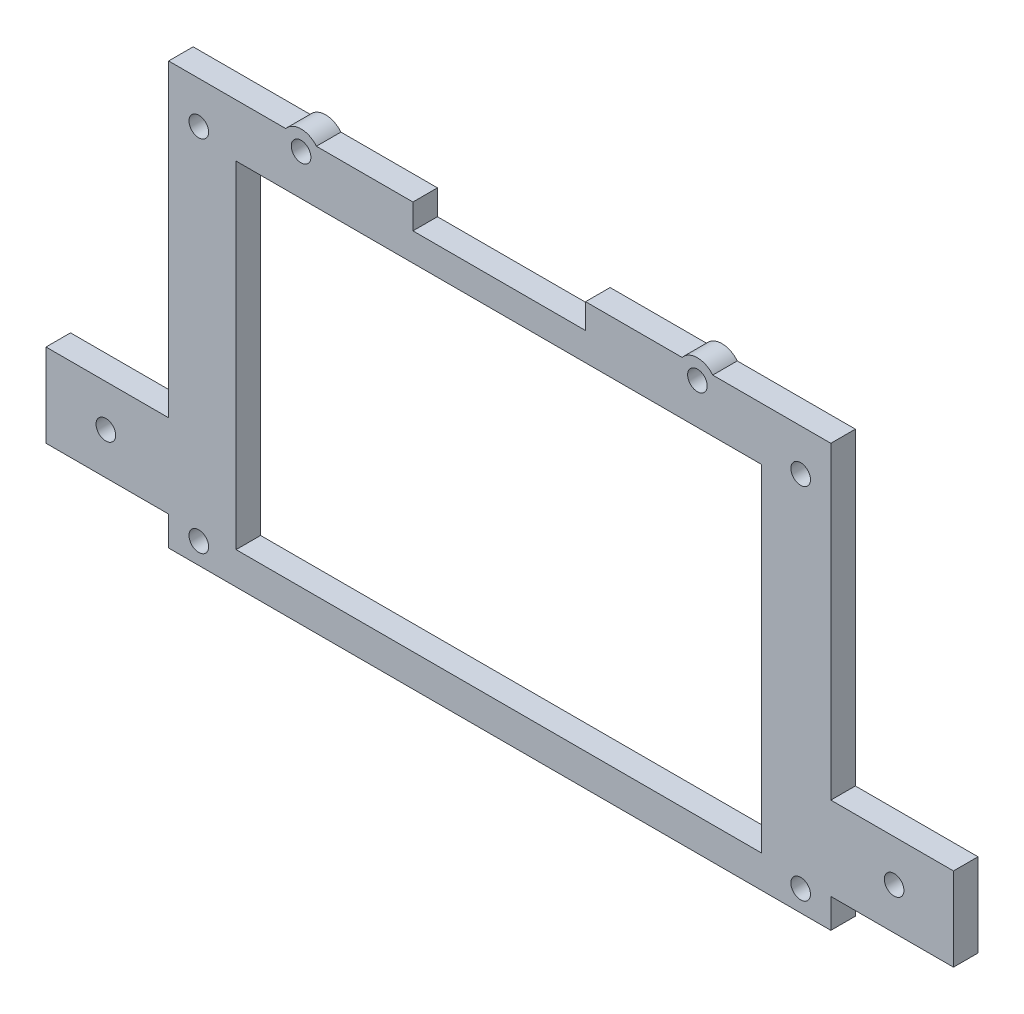
SolidWorks part; units mm, degrees
ref_plane "Front Plane" through (0, 0, 0) normal (0, 0, 1) x (1, 0, 0)
ref_plane "Top Plane" through (0, 0, 0) normal (0, 1, 0) x (1, 0, 0)
ref_plane "Right Plane" through (0, 0, 0) normal (1, 0, 0) x (0, 0, -1)
sketch "Sketch1" plane through (0, 0, 0) normal (0, 0, 1) x (1, 0, 0)
  line L1 (67.5, -43) -> (-67.5, -43)
  line L2 (67.5, -43) -> (67.5, 43)
  line L3 (67.5, 43) -> (-67.5, 43)
  line L4 (-67.5, -43) -> (-67.5, 43)
  line L5 (67.5, -43) -> (-67.5, 43) construction
  line L6 (67.5, 43) -> (-67.5, -43) construction
  point P0 (0, 0)
  dimension "D1" = 135
  dimension "D2" = 86
extrude "Boss-Extrude1" add sketch "Sketch1" along normal blind 5
sketch "Sketch2" plane through (0, 0, 0) normal (0, 0, -1) x (-1, 0, 0)
  line L0 (0.1, 43) -> (0.1, 37.9) construction
  line L1 (-67.5, 43) -> (67.5, 43) construction
  line L2 (67.5, 43) -> (67.5, -43) construction
  line L8 (17.7, 43) -> (-17.5, 43)
  line L9 (-17.5, 43) -> (-17.5, 37.9)
  line L10 (-17.5, 37.9) -> (17.7, 37.9)
  line L11 (17.7, 37.9) -> (17.7, 43)
  dimension "D1" = 17.6
  dimension "D2" = 5.1
  dimension "D3" = 49.8
extrude "Cut-Extrude1" cut sketch "Sketch2" against normal blind 5
sketch "Sketch3" plane through (0, 0, 0) normal (0, 0, -1) x (-1, 0, 0)
  line L0 (67.5, -43) -> (-67.5, -43) construction
  line L1 (67.5, -37) -> (92.5, -37)
  line L2 (67.5, -37) -> (67.5, -20)
  line L3 (67.5, -20) -> (92.5, -20)
  line L4 (92.5, -37) -> (92.5, -20)
  line L5 (67.5, 43) -> (67.5, -43) construction
  line L6 (0, 0) -> (0, -27.1383) construction
  line L7 (-92.5, -37) -> (-92.5, -20)
  line L8 (-67.5, -20) -> (-92.5, -20)
  line L9 (-67.5, -37) -> (-67.5, -20)
  line L10 (-67.5, -37) -> (-92.5, -37)
  dimension "D1" = 6
  dimension "D2" = 25
  dimension "D3" = 17
extrude "Boss-Extrude2" add sketch "Sketch3" against normal blind 5
sketch "Sketch4" plane through (0, 0, 0) normal (0, 0, -1) x (-1, 0, 0)
  line L8 (-53.35, 32.2) -> (-53.35, -36.4)
  line L9 (-53.35, -36.4) -> (53.75, -36.4)
  line L10 (53.75, -36.4) -> (53.75, 32.2)
  line L11 (53.75, 32.2) -> (-53.35, 32.2)
  dimension "D1" = 32.2
  dimension "D2" = 36.4
  dimension "D3" = 53.35
  dimension "D4" = 53.75
extrude "Cut-Extrude2" cut sketch "Sketch4" against normal blind 5
sketch "Sketch5" plane through (0, 0, 0) normal (0, 0, -1) x (-1, 0, 0)
  circle A0 centre (-40.3, 40.5) radius 2
  circle A1 centre (-80.4, -28.5) radius 2
  circle A2 centre (80.3, -28.5) radius 2
  circle A3 centre (40.5, 40.5) radius 2
  dimension "D1" = 4
  dimension "D2" = 4
  dimension "D3" = 4
  dimension "D4" = 4
extrude "Cut-Extrude3" cut sketch "Sketch5" against normal blind 10
sketch "Sketch6" plane through (0, 0, 0) normal (0, 0, -1) x (-1, 0, 0)
  circle A0 centre (40.5, 40.5) radius 2
  circle A1 centre (40.5, 40.5) radius 4
  circle A2 centre (-40.3, 40.5) radius 2
  circle A3 centre (-40.3, 40.5) radius 4
  dimension "D1" = 8
  dimension "D2" = 8
extrude "Boss-Extrude3" add sketch "Sketch6" against normal blind 5
sketch "Sketch7" plane through (0, 0, 0) normal (0, 0, -1) x (-1, 0, 0)
  circle A4 centre (61.35, -38.7) radius 2
  circle A5 centre (-61.35, -38.7) radius 2
  circle A6 centre (-61.35, 34.5) radius 2
  circle A7 centre (61.35, 34.5) radius 2
  dimension "D1" = 4
  dimension "D2" = 4
  dimension "D3" = 4
  dimension "D4" = 4
extrude "Cut-Extrude4" cut sketch "Sketch7" against normal blind 5
